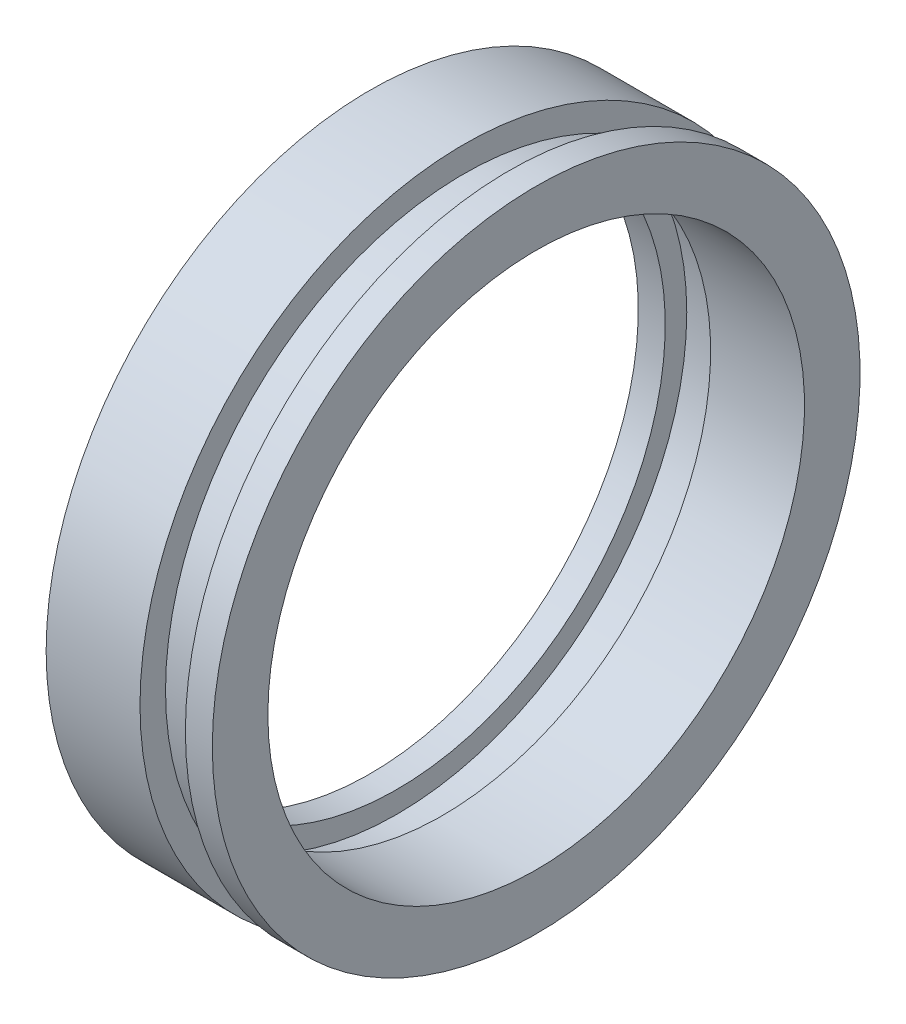
SolidWorks part; units mm, degrees
material "6061-T6 (SS)"
ref_plane "Front Plane" through (0, 0, 0) normal (0, 0, 1) x (1, 0, 0)
ref_plane "Top Plane" through (0, 0, 0) normal (0, 1, 0) x (1, 0, 0)
ref_plane "Right Plane" through (0, 0, 0) normal (1, 0, 0) x (0, 0, -1)
sketch "Sketch1" plane through (0, 0, 0) normal (0, 0, 1) x (1, 0, 0)
  line L0 (0, 28.829) -> (0, 34.798)
  line L1 (0, 34.798) -> (10.0838, 34.798)
  line L2 (10.0838, 34.798) -> (10.0838, 32.0548)
  line L3 (10.0838, 32.0548) -> (14.9606, 32.0548)
  line L4 (14.9606, 32.0548) -> (14.9606, 34.798)
  line L5 (14.9606, 34.798) -> (17.8562, 34.798)
  line L6 (17.8562, 34.798) -> (17.8562, 28.829)
  line L7 (17.8562, 28.829) -> (7.7724, 28.829)
  line L8 (7.7724, 28.829) -> (7.7724, 31.1404)
  line L9 (7.7724, 31.1404) -> (2.8956, 31.1404)
  line L10 (2.8956, 31.1404) -> (2.8956, 28.829)
  line L11 (2.8956, 28.829) -> (0, 28.829)
  line L12 (0, 0) -> (17.8562, 0) construction
  dimension "D1" = 17.8562
  dimension "D2" = 4.8768
  dimension "D3" = 4.8768
  dimension "D4" = 2.3114
  dimension "D5" = 2.7432
  dimension "D6" = 34.798
  dimension "D7" = 28.829
  dimension "D9" = 2.8956
  dimension "D8" = 2.8956
revolve "Revolve1" add sketch "Sketch1" angle 360 about L12
equation "\"D8@Sketch1\"=\"D9@Sketch1\""
equation "\"D7@Sketch1\"=2.27/2"
equation "\"D6@Sketch1\"=2.74/2"
